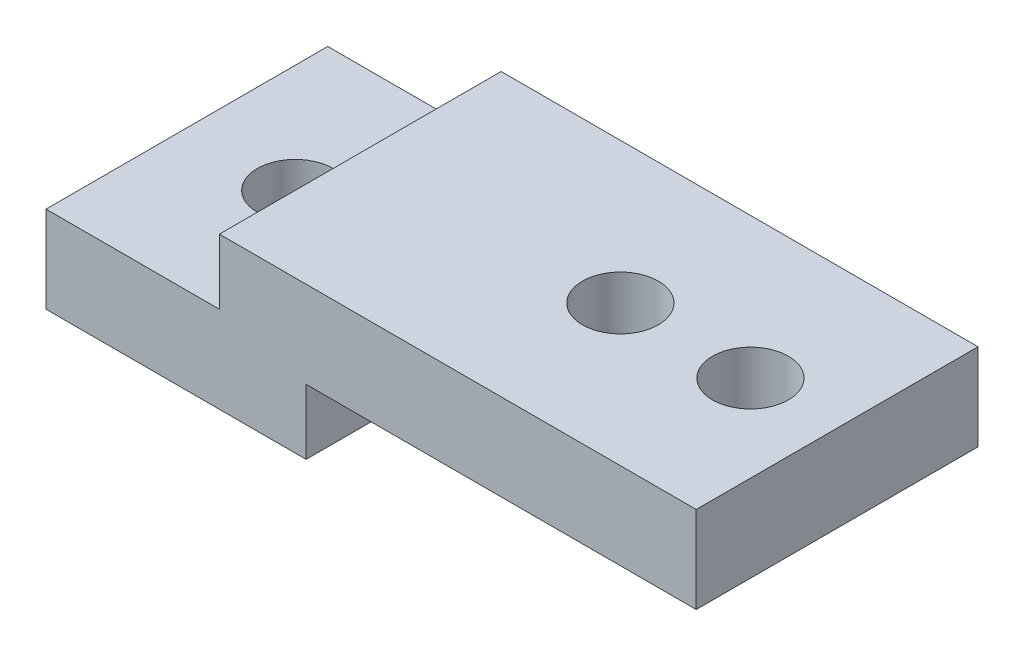
SolidWorks part; units mm, degrees
ref_plane "Front Plane" through (0, 0, 0) normal (0, 0, 1) x (1, 0, 0)
ref_plane "Top Plane" through (0, 0, 0) normal (0, 1, 0) x (1, 0, 0)
ref_plane "Right Plane" through (0, 0, 0) normal (1, 0, 0) x (0, 0, -1)
sketch "Sketch1" plane through (0, 0, 0) normal (0, 1, 0) x (1, 0, 0)
  line L1 (0, 13) -> (30, 13)
  line L2 (0, 13) -> (0, 0)
  line L3 (0, 0) -> (30, 0)
  line L4 (30, 13) -> (30, 0)
  point P4 (0, 0)
  dimension "D1" = 30
  dimension "D2" = 13
extrude "Boss-Extrude1" add sketch "Sketch1" along normal blind 4
sketch "Sketch2" plane through (0, 0, 0) normal (0, 0, 1) x (1, 0, 0)
  line L0 (0, 0) -> (30, 0) construction
  line L1 (30, 0) -> (12, 0)
  line L2 (30, 0) -> (30, 3)
  line L3 (30, 3) -> (12, 3)
  line L4 (12, 0) -> (12, 3)
  line L5 (0, 4) -> (0, 0) construction
  line L7 (30, 4) -> (30, 0) construction
  dimension "D1" = 3
  dimension "D2" = 12
extrude "Cut-Extrude1" cut sketch "Sketch2" against normal through all
sketch "Sketch3" plane through (0, 4, 0) normal (0, 1, 0) x (1, 0, 0)
  line L0 (0, 0) -> (30, 0) construction
  line L1 (30, 0) -> (8, 0)
  line L2 (30, 0) -> (30, 13)
  line L3 (30, 13) -> (8, 13)
  line L4 (8, 0) -> (8, 13)
  line L5 (30, 0) -> (30, 13) construction
  line L6 (30, 13) -> (0, 13) construction
  dimension "D1" = 22
extrude "Boss-Extrude2" add sketch "Sketch3" along normal blind 3
sketch "Sketch4" plane through (0, 4, 0) normal (0, 1, 0) x (1, 0, 0)
  line L0 (0, 13) -> (0, 0) construction
  circle A0 centre (5, 6.5) radius 1.75
  point P4 (0, 0)
  point P5 (0, 6.5)
  dimension "D1" = 3.5
  dimension "D2" = 5
extrude "Cut-Extrude2" cut sketch "Sketch4" against normal through all
sketch "Sketch7" plane through (0, 7, 0) normal (0, 1, 0) x (1, 0, 0)
  line L0 (8, 13) -> (8, 0) construction
  line L1 (30, 0) -> (30, 13) construction
  circle A0 centre (20, 6.5) radius 1.75
  circle A1 centre (26, 6.5) radius 1.75
  point P4 (8, 6.5)
  dimension "D1" = 3.5
  dimension "D3" = 3.5
  dimension "D2" = 12
  dimension "D4" = 4
extrude "Cut-Extrude5" cut sketch "Sketch7" against normal through all
